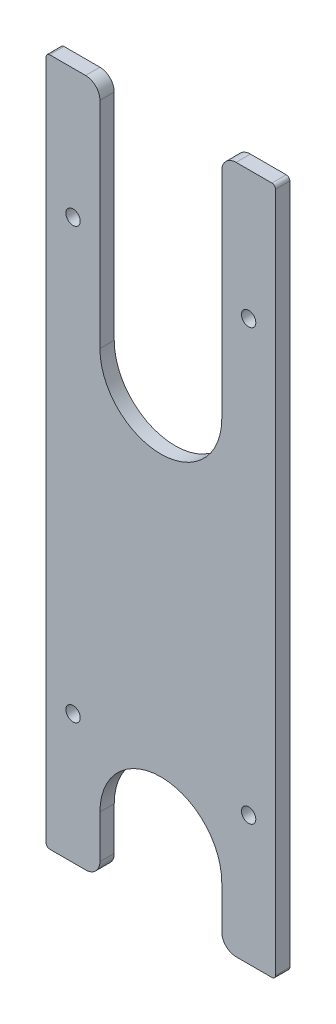
SolidWorks part; units mm, degrees
material "Acrylic (Medium-high impact)"
ref_plane "Front Plane" through (0, 0, 0) normal (0, 0, 1) x (1, 0, 0)
ref_plane "Top Plane" through (0, 0, 0) normal (0, 1, 0) x (1, 0, 0)
ref_plane "Right Plane" through (0, 0, 0) normal (1, 0, 0) x (0, 0, -1)
sketch "Sketch1" plane through (0, 0, 0) normal (0, 0, 1) x (1, 0, 0)
  line L0 (-26.9875, 50.8) -> (-26.9875, 152.4)
  line L1 (50.8, 127) -> (-50.8, 127) construction
  line L2 (50.8, 127) -> (50.8, -127) construction
  line L3 (50.8, -127) -> (-50.8, -127) construction
  line L4 (-50.8, 127) -> (-50.8, -127) construction
  line L5 (50.8, 127) -> (-50.8, -127) construction
  line L6 (50.8, -127) -> (-50.8, 127) construction
  line L7 (-50.8, 152.4) -> (-26.9875, 152.4)
  line L8 (-50.8, 152.4) -> (-50.8, -152.4)
  line L9 (-50.8, -152.4) -> (-26.9875, -152.4)
  line L10 (50.8, 152.4) -> (50.8, -152.4)
  line L11 (-50.8, 152.4) -> (50.8, -152.4) construction
  line L12 (-50.8, -152.4) -> (50.8, 152.4) construction
  line L14 (26.9875, 50.8) -> (26.9875, 152.4)
  line L15 (-26.9875, -127) -> (-26.9875, -152.4)
  line L16 (26.9875, -152.4) -> (50.8, -152.4)
  line L17 (26.9875, -127) -> (26.9875, -152.4)
  line L18 (26.9875, 152.4) -> (50.8, 152.4)
  arc A0 (-26.9875, 50.8) -> (26.9875, 50.8) centre (0, 50.8) ccw
  arc A1 (26.9875, -127) -> (-26.9875, -127) centre (0, -127) ccw
  point P0 (0, 0)
  point P10 (0, 0)
  dimension "D3" = 53.975
  dimension "D1" = 101.6
  dimension "D2" = 254
  dimension "D4" = 304.8
  dimension "D5" = 101.6
extrude "Boss-Extrude1" add sketch "Sketch1" along normal blind 6.35
sketch "Sketch2" plane through (0, 0, 6.35) normal (0, 0, 1) x (1, 0, 0)
  line L0 (-50.8, -152.4) -> (-26.9875, -152.4) construction
  line L1 (26.9875, -152.4) -> (50.8, -152.4) construction
  line L2 (-26.9875, 152.4) -> (-50.8, 152.4) construction
  point P0 (-38.8938, 95.25)
  point P1 (38.8937, 95.25)
  point P2 (38.8937, -95.25)
  point P3 (-38.8938, -95.25)
  point P6 (-38.8938, -152.4)
  point P10 (38.8937, -152.4)
  dimension "D1" = 57.15
  dimension "D2" = 57.15
hole_wizard "1/4 (0.2500) Dowel Hole1" positions "Sketch3" profile "Sketch4" hole size "1/4" standard "ANSI Inch" end condition up to next
sketch "Sketch3" plane through (0, 0, 6.35) normal (0, 0, 1) x (1, 0, 0)
  point P0 (-38.8938, 95.25)
  point P3 (38.8937, 95.25)
  point P6 (38.8937, -95.25)
  point P9 (-38.8938, -95.25)
sketch "Sketch4" plane through (-38.8938, 95.25, 6.35) normal (1, 0, 0) x (0, -1, 0)
  line L0 (0, 0) -> (0, 6.35)
  line L1 (0, 6.35) -> (3.175, 6.35)
  line L2 (3.175, 6.35) -> (3.175, 0)
  line L5 (3.175, 0) -> (0, 0)
  line L11 (0, -6.35) -> (0, 107.95) construction
  dimension "Thru Hole Dia." = 6.35
  dimension "Thru Hole Depth" = 6.35
fillet "Fillet1" radius 6.35 4 edges at (26.9875, -152.4, 3.175) (-26.9875, -152.4, 3.175) (26.9875, 152.4, 3.175) (-26.9875, 152.4, 3.175)
fillet "Fillet2" radius 1.5875 4 edges at (-50.8, -152.4, 3.175) (50.8, -152.4, 3.175) (-50.8, 152.4, 3.175) (50.8, 152.4, 3.175)
